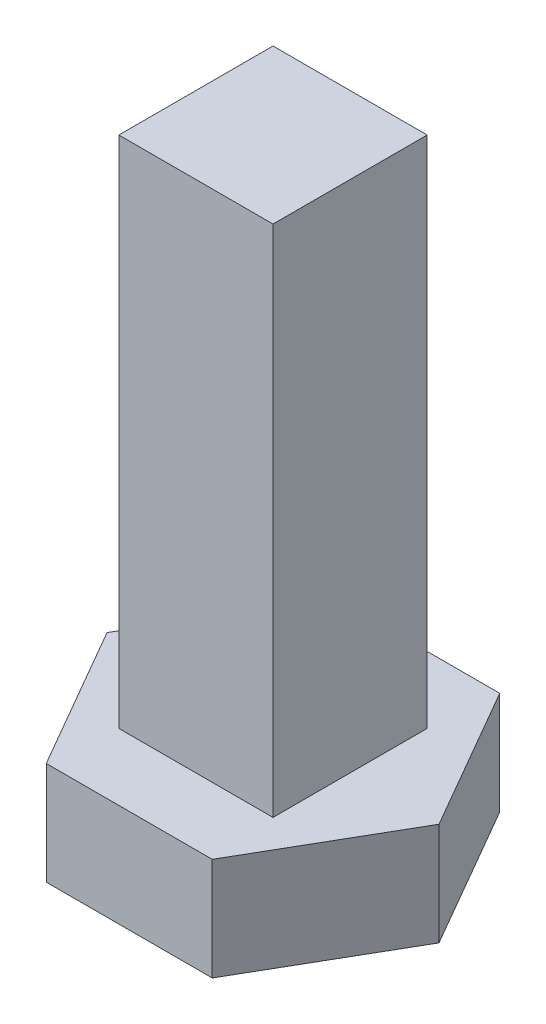
SolidWorks part; units mm, degrees
ref_plane "정면" through (0, 0, 0) normal (0, 0, 1) x (1, 0, 0)
ref_plane "윗면" through (0, 0, 0) normal (0, 1, 0) x (1, 0, 0)
ref_plane "우측면" through (0, 0, 0) normal (1, 0, 0) x (0, 0, -1)
sketch "스케치1" plane through (0, 0, 0) normal (0, 1, 0) x (1, 0, 0)
  line L1 (3.23, 0) -> (1.615, 2.7973)
  line L2 (1.615, 2.7973) -> (-1.615, 2.7973)
  line L3 (-1.615, 2.7973) -> (-3.23, 0)
  line L4 (-3.23, 0) -> (-1.615, -2.7973)
  line L5 (-1.615, -2.7973) -> (1.615, -2.7973)
  line L6 (1.615, -2.7973) -> (3.23, 0)
  circle A0 centre (0, 0) radius 2.7973 construction
  dimension "D1" = 3.23
extrude "보스-돌출1" add sketch "스케치1" along normal blind 2
sketch "스케치2" plane through (0, 2, 0) normal (0, 1, 0) x (1, 0, 0)
  line L1 (-1.5, 1.5) -> (1.5, 1.5)
  line L2 (-1.5, 1.5) -> (-1.5, -1.5)
  line L3 (-1.5, -1.5) -> (1.5, -1.5)
  line L4 (1.5, 1.5) -> (1.5, -1.5)
  line L5 (-1.5, 1.5) -> (1.5, -1.5) construction
  line L6 (-1.5, -1.5) -> (1.5, 1.5) construction
  dimension "D2" = 3
  dimension "D3" = 3
extrude "보스-돌출2" add sketch "스케치2" along normal blind 10
